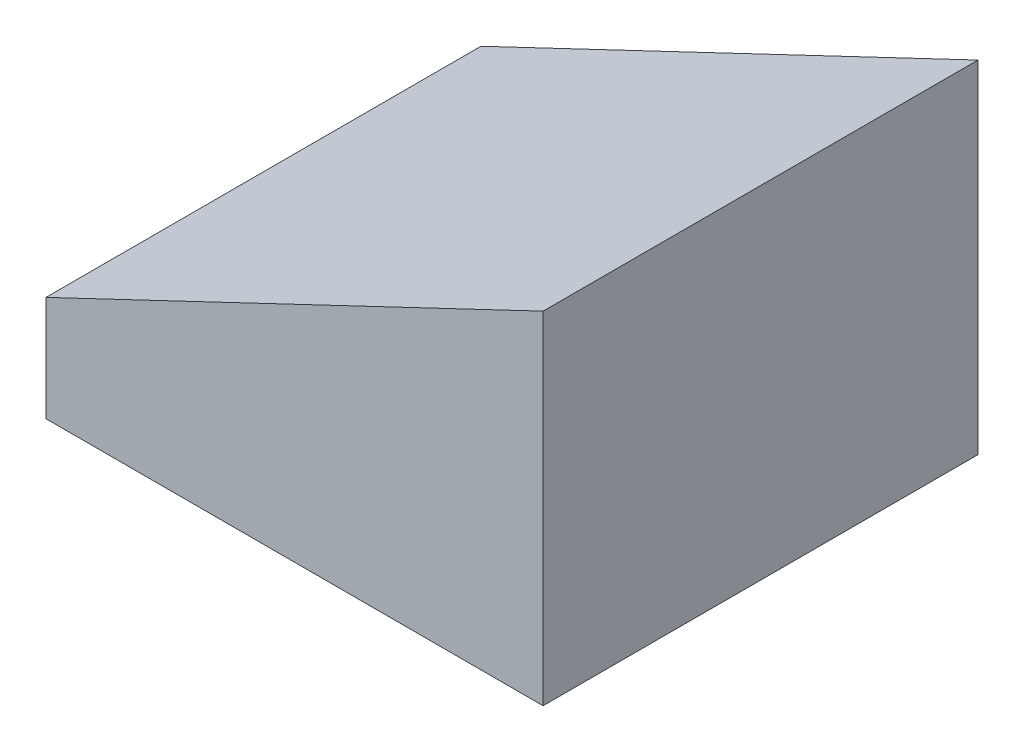
SolidWorks part; units mm, degrees
material "ABS"
ref_plane "Front Plane" through (0, 0, 0) normal (0, 0, 1) x (1, 0, 0)
ref_plane "Top Plane" through (0, 0, 0) normal (0, 1, 0) x (1, 0, 0)
ref_plane "Right Plane" through (0, 0, 0) normal (1, 0, 0) x (0, 0, -1)
sketch "Sketch1" plane through (0, 0, 0) normal (0, 0, 1) x (1, 0, 0)
  line L0 (-5.08, 0) -> (5.08, 0)
  line L1 (5.08, 0) -> (5.08, -3.175)
  line L2 (5.08, -3.175) -> (-5.08, -3.175)
  line L3 (-5.08, -3.175) -> (-5.08, 0)
  point P3 (0, -3.175)
  dimension "D1" = 10.16
  dimension "D2" = 3.175
extrude "Boss-Extrude1" add sketch "Sketch1" along normal mid plane 8.89
sketch "Sketch3" plane through (0, -3.175, 0) normal (0, -1, 0) x (1, 0, 0)
  line L0 (-2.54, 2.54) -> (-2.54, -2.54)
  line L1 (-2.54, -2.54) -> (2.54, -2.54)
  line L2 (2.54, -2.54) -> (2.54, 2.54)
  line L3 (2.54, 2.54) -> (-2.54, 2.54)
  line L4 (-5.08, -4.445) -> (5.08, -4.445)
  line L5 (5.08, -4.445) -> (5.08, 4.445)
  line L6 (5.08, 4.445) -> (-5.08, 4.445)
  line L7 (-5.08, 4.445) -> (-5.08, -4.445)
  line L8 (-5.08, -4.445) -> (5.08, -4.445)
  line L9 (5.08, -4.445) -> (5.08, 4.445)
  line L10 (5.08, 4.445) -> (-5.08, 4.445)
  line L11 (-5.08, 4.445) -> (-5.08, -4.445)
  dimension "D1" = 0
extrude "Cut-Extrude1" cut sketch "Sketch3" against normal blind 1.905 flip side to cut
sketch "Sketch5" plane through (0, 0, 0) normal (0, 0, 1) x (1, 0, 0)
  line L0 (-2.9244, 0) -> (5.08, 3.81)
  line L2 (5.08, 0) -> (5.08, 3.81)
  line L4 (5.08, 0) -> (-5.08, 0) construction
  line L5 (5.08, 0) -> (-2.9244, 0)
  dimension "D1" = 3.81
extrude "Boss-Extrude2" add sketch "Sketch5" along normal up to surface and the other way up to surface up to face at (0, -1.5875, 4.445) other way up to face at (0, -1.5875, -4.445)
sketch "Sketch6" plane through (0, 0, 0) normal (0, 0, 1) x (1, 0, 0)
  line L1 (-5.08, -1.026) -> (-5.08, 0)
  line L5 (-2.9244, 0) -> (-5.08, -1.026)
  line L6 (-2.9244, 0) -> (5.08, 3.81) construction
  line L7 (-2.9244, 0) -> (-5.08, 0)
extrude "Cut-Extrude3" cut sketch "Sketch6" against normal through all both and the other way through all
